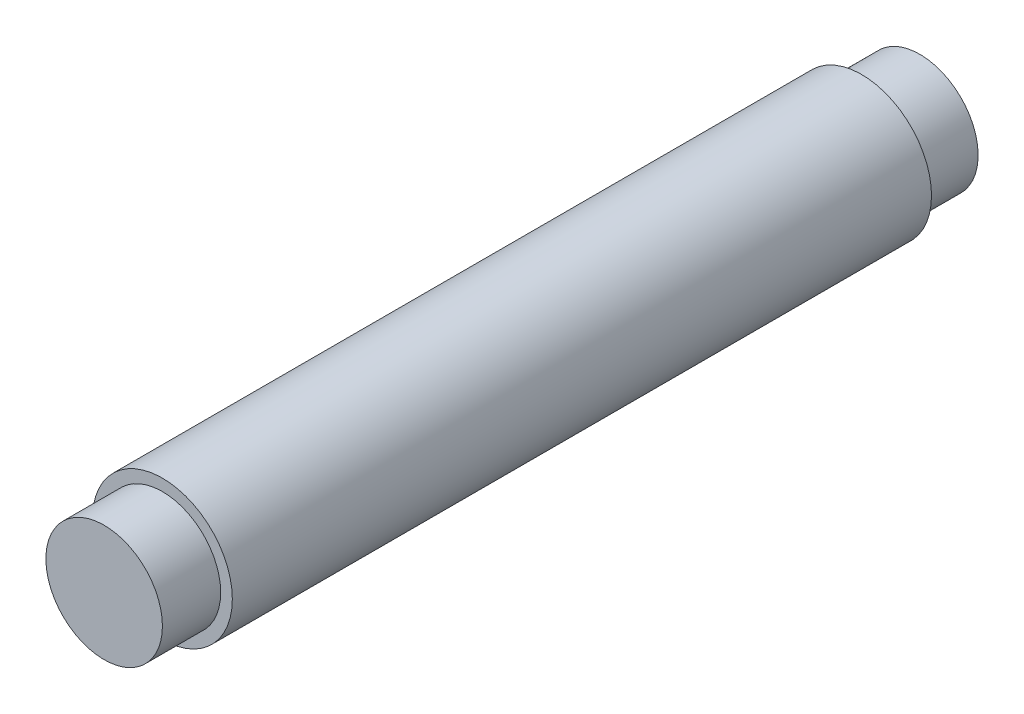
SolidWorks part; units mm, degrees
material "Plain Carbon Steel"
ref_plane "Front Plane" through (0, 0, 0) normal (0, 0, 1) x (1, 0, 0)
ref_plane "Top Plane" through (0, 0, 0) normal (0, 1, 0) x (1, 0, 0)
ref_plane "Right Plane" through (0, 0, 0) normal (1, 0, 0) x (0, 0, -1)
sketch "Sketch1" plane through (0, 0, 0) normal (0, 0, 1) x (1, 0, 0)
  circle A0 centre (0, 0) radius 6
  dimension "D1" = 12
extrude "Boss-Extrude1" add sketch "Sketch1" along normal blind 60
sketch "Sketch2" plane through (0, 0, 60) normal (0, 0, 1) x (1, 0, 0)
  circle A0 centre (0, 0) radius 5
  dimension "D1" = 10
extrude "Boss-Extrude2" add sketch "Sketch2" along normal blind 5
sketch "Sketch3" plane through (0, 0, 0) normal (0, 0, -1) x (-1, 0, 0)
  circle A0 centre (0, 0) radius 5
  dimension "D1" = 10
extrude "Boss-Extrude3" add sketch "Sketch3" along normal blind 5
